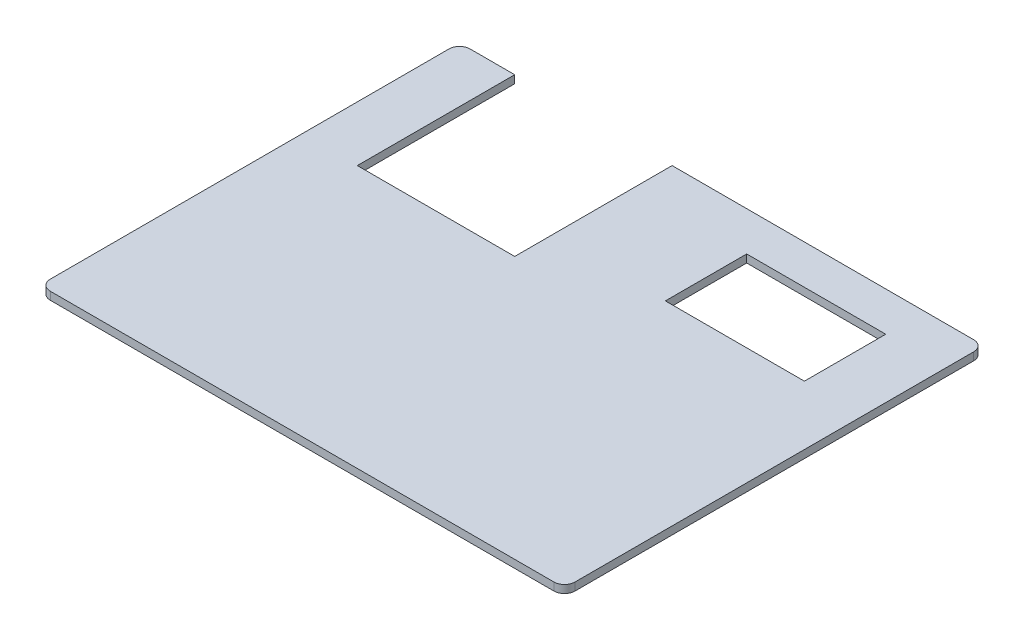
SolidWorks part; units mm, degrees
ref_plane "Front Plane" through (0, 0, 0) normal (0, 0, 1) x (1, 0, 0)
ref_plane "Top Plane" through (0, 0, 0) normal (0, 1, 0) x (1, 0, 0)
ref_plane "Right Plane" through (0, 0, 0) normal (1, 0, 0) x (0, 0, -1)
sketch "Sketch1" plane through (0, 0, 0) normal (0, 1, 0) x (1, 0, 0)
  line L1 (-27.0627, 48.8119) -> (72.9373, 48.8119)
  line L2 (-27.0627, 48.8119) -> (-27.0627, -31.1881)
  line L3 (-27.0627, -31.1881) -> (72.9373, -31.1881)
  line L4 (72.9373, 48.8119) -> (72.9373, -31.1881)
  dimension "D1" = 100
  dimension "D2" = 80
extrude "Boss-Extrude1" add sketch "Sketch1" along normal blind 1.5
fillet "Fillet1" radius 2 4 edges at (-27.0627, 0.75, 31.1881) (-27.0627, 0.75, -48.8119) (72.9373, 0.75, -48.8119) (72.9373, 0.75, 31.1881)
sketch "Sketch7" plane through (0, 1.5, 0) normal (0, 1, 0) x (1, 0, 0)
  line L1 (70.9373, 48.8119) -> (-25.0627, 48.8119) construction
  line L2 (-16.5458, 48.8119) -> (13.4542, 48.8119)
  line L3 (-16.5458, 48.8119) -> (-16.5458, 18.8119)
  line L4 (-16.5458, 18.8119) -> (13.4542, 18.8119)
  line L5 (13.4542, 48.8119) -> (13.4542, 18.8119)
  point P9 (10.5535, 18.8119)
  point P10 (13.4542, 18.8119)
  dimension "D1" = 30
  dimension "D2" = 30
extrude "bukaan" cut sketch "Sketch7" against normal blind 7.5
sketch "Sketch8" plane through (0, 0, 0) normal (0, 1, 0) x (1, 0, 0)
  line L1 (35.1505, 41.3332) -> (61.6505, 41.3332)
  line L2 (35.1505, 41.3332) -> (35.1505, 25.8332)
  line L3 (35.1505, 25.8332) -> (61.6505, 25.8332)
  line L4 (61.6505, 41.3332) -> (61.6505, 25.8332)
  point P4 (61.6505, 41.3332)
  dimension "D1" = 15.5
  dimension "D2" = 26.5
extrude "Cut-Extrude6" cut sketch "Sketch8" along normal blind 10.5
